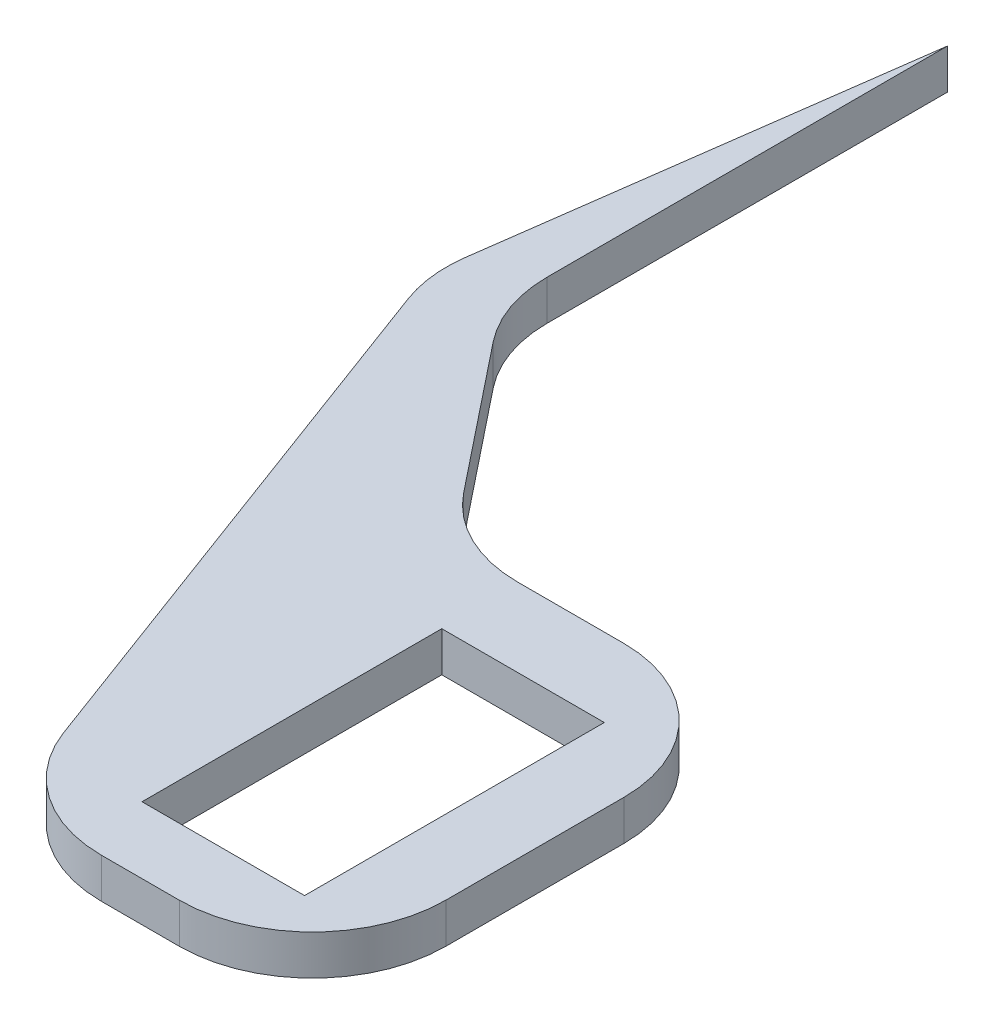
SolidWorks part; units mm, degrees
ref_plane "Front Plane" through (0, 0, 0) normal (0, 0, 1) x (1, 0, 0)
ref_plane "Top Plane" through (0, 0, 0) normal (0, 1, 0) x (1, 0, 0)
ref_plane "Right Plane" through (0, 0, 0) normal (1, 0, 0) x (0, 0, -1)
sketch "Sketch1" plane through (0, 0, 0) normal (0, 1, 0) x (1, 0, 0)
  line L1 (-11.1, 17.1285) -> (11.7, 17.1285) construction
  line L2 (-11.1, 17.1285) -> (-11.1, -16.25) construction
  line L3 (-11.1, -16.25) -> (11.7, -16.25)
  line L4 (11.7, 17.1285) -> (11.7, -16.25)
  line L7 (-6.1, 11.25) -> (6.1, 11.25)
  line L8 (-6.1, 11.25) -> (-6.1, -11.25)
  line L9 (-6.1, -11.25) -> (6.1, -11.25)
  line L10 (6.1, 11.25) -> (6.1, -11.25)
  line L11 (-6.1, 11.25) -> (6.1, -11.25) construction
  line L12 (-6.1, -11.25) -> (6.1, 11.25) construction
  line L15 (0, 0) -> (0, 83.4884) construction
  line L16 (-25, 83.4884) -> (-25, -24.3562) construction
  line L18 (-25, 34.5653) -> (-25, 68.107)
  line L19 (-25, 68.107) -> (-29.6854, 33.7997)
  line L20 (-29.6854, 33.7997) -> (-11.1, -16.25)
  line L21 (-25, 34.5653) -> (-11.1, 17.1285)
  line L22 (-11.1, 17.1285) -> (11.7, 17.1285)
  point P0 (0, 0)
  point P6 (0, 0)
  dimension "D1" = 22.5
  dimension "D2" = 12.2
  dimension "D3" = 0
  dimension "D5" = 5
  dimension "D6" = 5
  dimension "D7" = 5.6
extrude "Boss-Extrude1" add sketch "Sketch1" along normal blind 3
fillet "Fillet2" radius 10 6 edges at (-29.6854, 1.5, -33.7997) (-25, 1.5, -34.5653) (-11.1, 1.5, 16.25) (11.7, 1.5, 16.25) (-11.1, 1.5, -17.1285) (11.7, 1.5, -17.1285)
